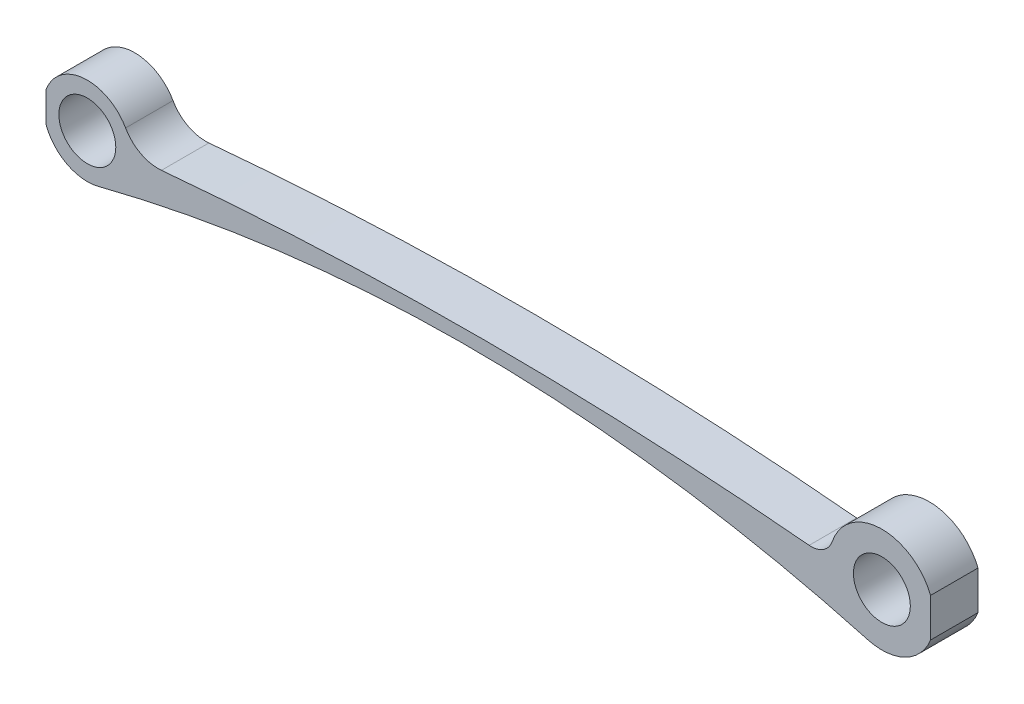
SolidWorks part; units mm, degrees
material "ABS"
ref_plane "Płaszczyzna przednia" through (0, 0, 0) normal (0, 0, 1) x (1, 0, 0)
ref_plane "Płaszczyzna górna" through (0, 0, 0) normal (0, 1, 0) x (1, 0, 0)
ref_plane "Płaszczyzna prawa" through (0, 0, 0) normal (1, 0, 0) x (0, 0, -1)
sketch "Szkic1" plane through (0, 0, 0) normal (0, 0, 1) x (1, 0, 0)
  line L0 (-3, 0) -> (83.7624, 0) construction
  line L1 (40.3812, 0) -> (40.3812, 21.7565) construction
  circle A0 centre (0, 0) radius 3
  circle A1 centre (83.7624, 0) radius 3
  arc A2 (82.2884, -5.3223) -> (78.5373, 1.7882) centre (83.7624, 0) ccw
  arc A3 (4.0339, 2.2831) -> (1.1454, -4.4914) centre (0, 0) ccw
  arc A4 (82.2884, -5.3223) -> (1.1454, -4.4914) centre (40.1549, -157.4605) ccw
  arc A5 (76.0921, 0.2083) -> (78.5373, 1.7882) centre (76.3124, 2.5496) ccw
  arc A6 (76.0921, 0.2083) -> (7.8136, 0.3038) centre (41.4375, -368.2075) ccw
  arc A7 (4.0339, 2.2831) -> (7.8136, 0.3038) centre (7.4563, 4.2201) ccw
  point P10 (4.6352, 0)
  point P12 (78.2398, 0)
  dimension "D1" = 83.7624
  dimension "D2" = 6
  dimension "D3" = 5.5226
  dimension "D4" = 4.6352
  dimension "D5" = 6
  dimension "D6" = 2.3516
  dimension "D8" = 3.9325
extrude "Dodanie-wyciągnięcie1" add sketch "Szkic1" along normal blind 5
sketch "Szkic2" plane through (0, 0, 0) normal (0, 0, 1) x (1, 0, 0)
  line L0 (196.2931, 0) -> (-6.6873, 0) construction
  line L1 (88.8955, 4.1341) -> (88.8955, -3.3715)
  line L2 (-4.3568, -2.5646) -> (-4.3568, 2.4871)
  line L4 (-4.3568, 2.4871) -> (-5.0086, 2.4871)
  line L5 (-4.3568, 2.4871) -> (-4.3568, -2.5646)
  line L6 (-4.3568, -2.5646) -> (-5.0086, -2.5646)
  line L7 (-5.0086, 2.4871) -> (-5.0086, -2.5646)
  line L8 (88.8955, -3.3715) -> (194.4479, -3.3715)
  line L9 (88.8955, -3.3715) -> (88.8955, 4.1341)
  line L10 (88.8955, 4.1341) -> (194.4479, 4.1341)
  line L11 (194.4479, -3.3715) -> (194.4479, 4.1341)
extrude "Wytnij-wyciągnięcie3" cut sketch "Szkic2" along normal through all contours L0 L11 L10 L1 | L11 L0 L9 L8 | L0 L5 L4 L7 | L2 L0 L7 L6
